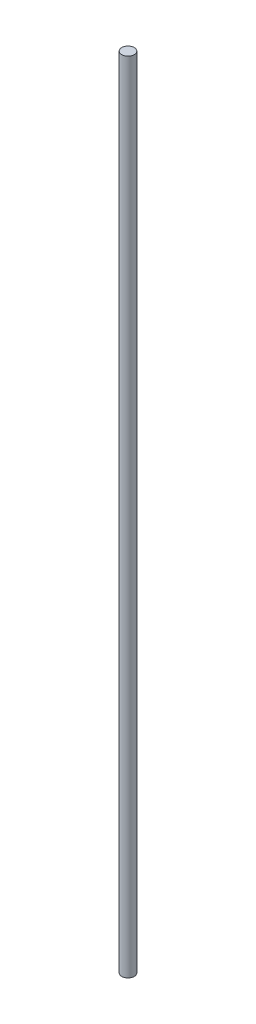
SolidWorks part; units mm, degrees
ref_plane "Front Plane" through (0, 0, 0) normal (0, 0, 1) x (1, 0, 0)
ref_plane "Top Plane" through (0, 0, 0) normal (0, 1, 0) x (1, 0, 0)
ref_plane "Right Plane" through (0, 0, 0) normal (1, 0, 0) x (0, 0, -1)
sketch "Sketch1" plane through (0, 0, 0) normal (0, 1, 0) x (1, 0, 0)
  circle A0 centre (0, 0) radius 4.7625
  dimension "D1" = 9.525
extrude "Boss-Extrude1" add sketch "Sketch1" along normal blind 609.6
